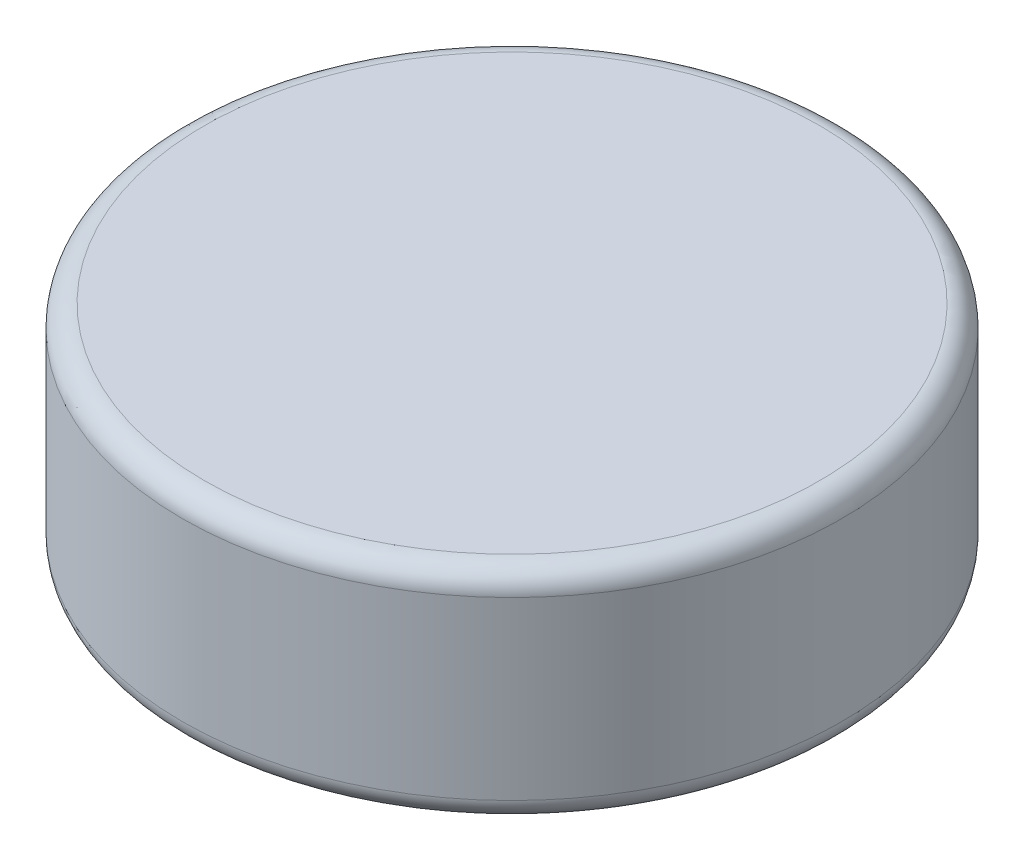
SolidWorks part; units mm, degrees
ref_plane "前视基准面" through (0, 0, 0) normal (0, 0, 1) x (1, 0, 0)
ref_plane "上视基准面" through (0, 0, 0) normal (0, 1, 0) x (1, 0, 0)
ref_plane "右视基准面" through (0, 0, 0) normal (1, 0, 0) x (0, 0, -1)
sketch "草图1" plane through (0, 0, 0) normal (0, 1, 0) x (1, 0, 0)
  circle A0 centre (0, 0) radius 3
  dimension "D1" = 6
extrude "凸台-拉伸1" add sketch "草图1" along normal blind 2
fillet "圆角1" radius 0.2 2 edges at (0, 0, 3) (0, 2, 3)
